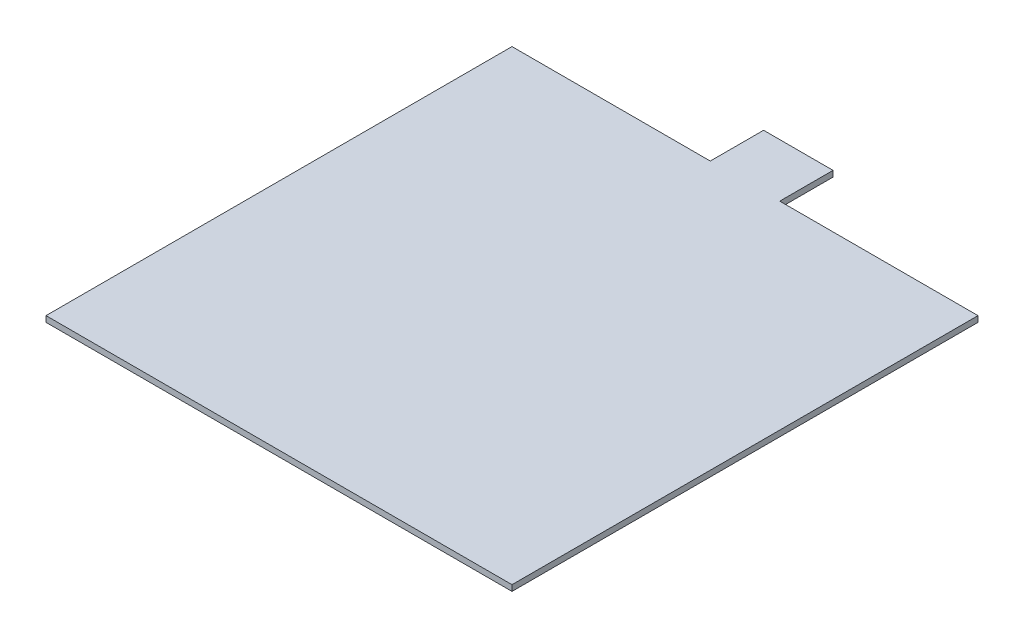
SolidWorks part; units mm, degrees
ref_plane "Front Plane" through (0, 0, 0) normal (0, 0, 1) x (1, 0, 0)
ref_plane "Top Plane" through (0, 0, 0) normal (0, 1, 0) x (1, 0, 0)
ref_plane "Right Plane" through (0, 0, 0) normal (1, 0, 0) x (0, 0, -1)
sketch "Sketch1" plane through (0, 0, 0) normal (0, 1, 0) x (1, 0, 0)
  line L1 (-21.85, -21.85) -> (21.85, -21.85)
  line L2 (-21.85, -21.85) -> (-21.85, 21.85)
  line L3 (-21.85, 21.85) -> (21.85, 21.85)
  line L4 (21.85, -21.85) -> (21.85, 21.85)
  line L5 (0, 21.85) -> (0, -21.85) construction
  line L6 (-21.85, 0) -> (21.85, 0) construction
  point P0 (0, 0)
  dimension "D1" = 43.7
  dimension "D2" = 43.7
extrude "Boss-Extrude1" add sketch "Sketch1" along normal blind 0.55
sketch "Sketch2" plane through (0, 0, 0) normal (0, 1, 0) x (1, 0, 0)
  line L0 (21.85, 21.85) -> (-21.85, 21.85) construction
  line L1 (-3.2564, 21.85) -> (3.2564, 21.85)
  line L2 (-3.2564, 21.85) -> (-3.2564, 26.85)
  line L3 (-3.2564, 26.85) -> (3.2564, 26.85)
  line L4 (3.2564, 21.85) -> (3.2564, 26.85)
  line L5 (0, -0.3025) -> (0, 0.3025) construction
  point P6 (0, 21.85)
  dimension "D1" = 5
extrude "Boss-Extrude2" add sketch "Sketch2" along normal blind 0.55
